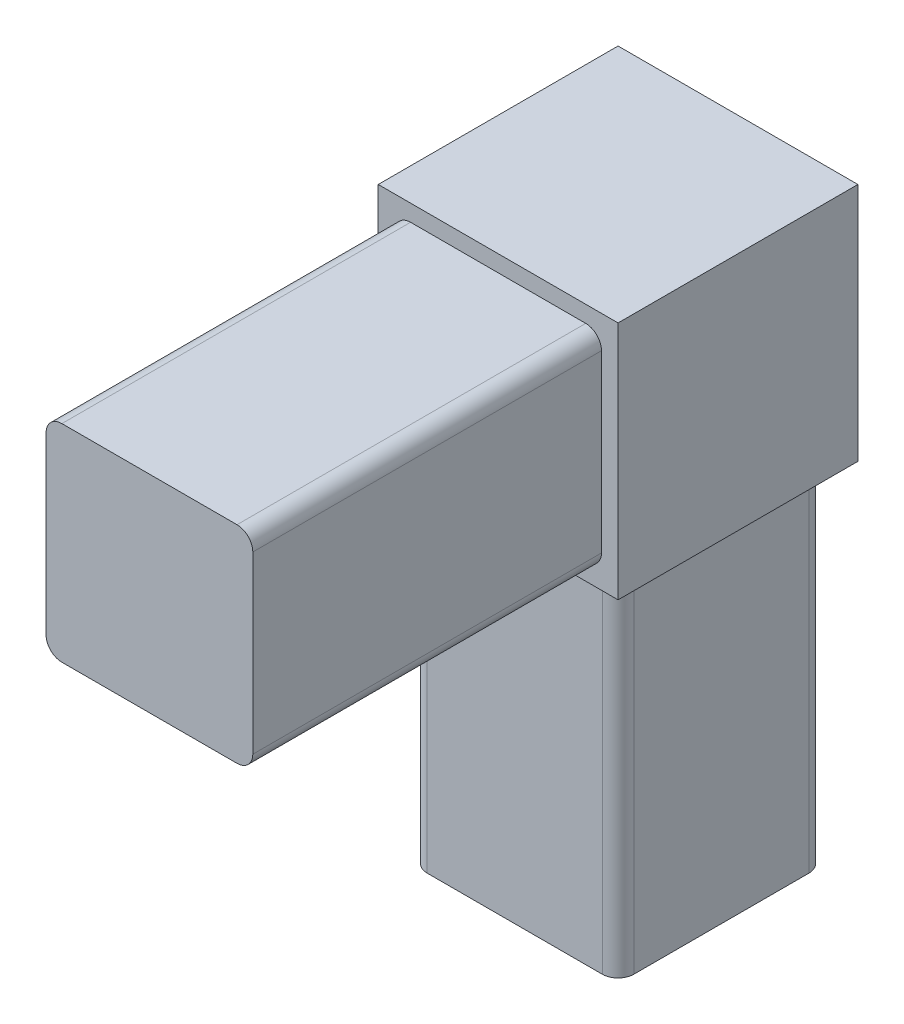
SolidWorks part; units mm, degrees
ref_plane "Front Plane" through (0, 0, 0) normal (0, 0, 1) x (1, 0, 0)
ref_plane "Top Plane" through (0, 0, 0) normal (0, 1, 0) x (1, 0, 0)
ref_plane "Right Plane" through (0, 0, 0) normal (1, 0, 0) x (0, 0, -1)
sketch "Sketch1" plane through (0, 0, 0) normal (0, 1, 0) x (1, 0, 0)
  line L1 (-8.3185, 8.3185) -> (8.3185, 8.3185)
  line L2 (-8.3185, 8.3185) -> (-8.3185, -8.3185)
  line L3 (-8.3185, -8.3185) -> (8.3185, -8.3185)
  line L4 (8.3185, 8.3185) -> (8.3185, -8.3185)
  line L5 (-8.3185, 8.3185) -> (8.3185, -8.3185) construction
  line L6 (-8.3185, -8.3185) -> (8.3185, 8.3185) construction
  point P0 (0, 0)
  dimension "D1" = 16.637
extrude "Boss-Extrude1" add sketch "Sketch1" along normal blind 28.067
sketch "Sketch2" plane through (0, 28.067, 0) normal (0, 1, 0) x (1, 0, 0)
  line L1 (-9.652, -9.652) -> (9.652, -9.652)
  line L2 (-9.652, -9.652) -> (-9.652, 9.652)
  line L3 (-9.652, 9.652) -> (9.652, 9.652)
  line L4 (9.652, -9.652) -> (9.652, 9.652)
  line L5 (-9.652, -9.652) -> (9.652, 9.652) construction
  line L6 (-9.652, 9.652) -> (9.652, -9.652) construction
  point P0 (0, 0)
  dimension "D1" = 19.304
  dimension "D2" = 19.304
extrude "Boss-Extrude2" add sketch "Sketch2" along normal blind 19.304
sketch "Sketch3" plane through (0, 0, 9.652) normal (0, 0, 1) x (1, 0, 0)
  line L0 (-9.652, 47.371) -> (9.652, 28.067) construction
  line L2 (-8.3185, 29.4005) -> (8.3185, 29.4005)
  line L3 (-8.3185, 29.4005) -> (-8.3185, 46.0375)
  line L4 (-8.3185, 46.0375) -> (8.3185, 46.0375)
  line L5 (8.3185, 29.4005) -> (8.3185, 46.0375)
  line L6 (-8.3185, 29.4005) -> (8.3185, 46.0375) construction
  line L7 (-8.3185, 46.0375) -> (8.3185, 29.4005) construction
  point P4 (0, 37.719)
  dimension "D1" = 16.637
extrude "Boss-Extrude3" add sketch "Sketch3" along normal blind 28.067
fillet "Fillet1" radius 1.27 8 edges at (8.3185, 46.0375, 23.6855) (8.3185, 29.4005, 23.6855) (-8.3185, 46.0375, 23.6855) (-8.3185, 29.4005, 23.6855) (-8.3185, 14.0335, 8.3185) (8.3185, 14.0335, 8.3185) (-8.3185, 14.0335, -8.3185) (8.3185, 14.0335, -8.3185)
